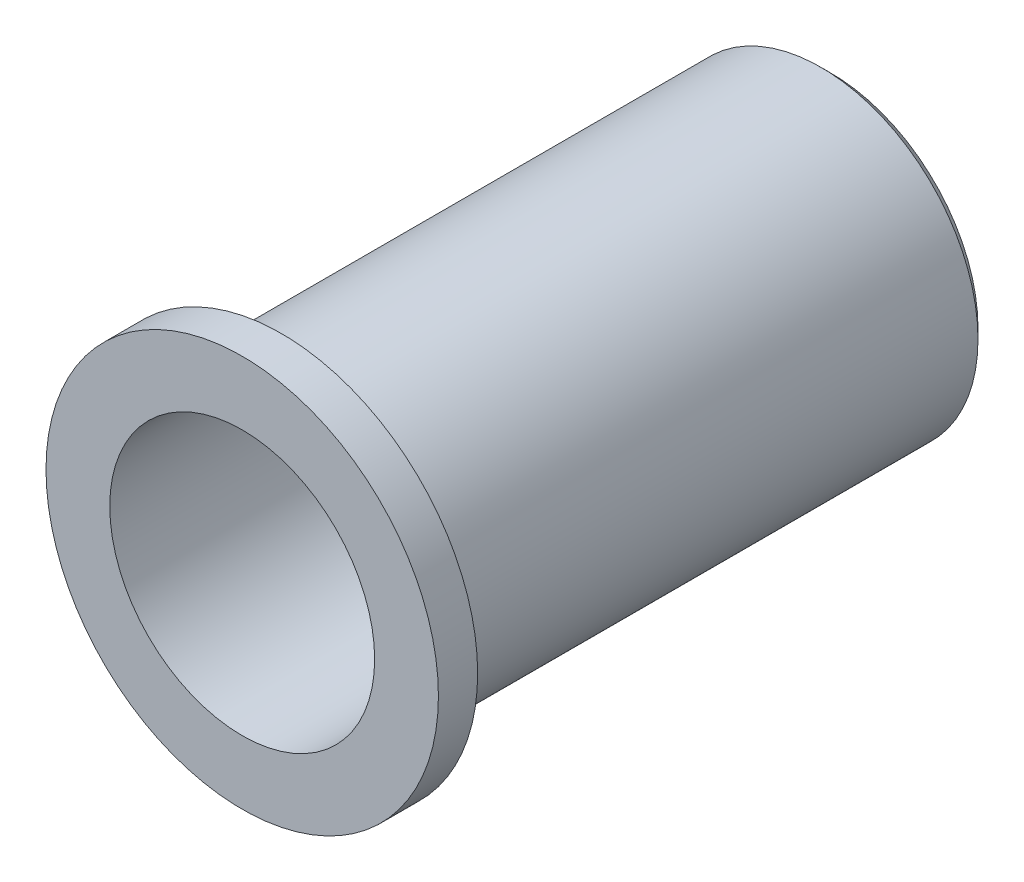
SolidWorks part; units mm, degrees
ref_plane "Спереди" through (0, 0, 0) normal (0, 0, 1) x (1, 0, 0)
ref_plane "Сверху" through (0, 0, 0) normal (0, 1, 0) x (1, 0, 0)
ref_plane "Справа" through (0, 0, 0) normal (1, 0, 0) x (0, 0, -1)
sketch "Эскиз1" plane through (0, 0, 0) normal (0, 0, 1) x (1, 0, 0)
  circle A0 centre (0, 0) radius 4
extrude "Бобышка-Вытянуть1" add sketch "Эскиз1" along normal blind 12
sketch "Эскиз2" plane through (0, 0, 12) normal (0, 0, 1) x (1, 0, 0)
  circle A0 centre (0, 0) radius 2.7
extrude "Вырез-Вытянуть1" cut sketch "Эскиз2" against normal blind 4.2
sketch "Эскиз3" plane through (0, 0, 0) normal (0, 0, -1) x (-1, 0, 0)
  circle A0 centre (0, 0) radius 3.2
extrude "Вырез-Вытянуть2" cut sketch "Эскиз3" against normal blind 11.2 flip side to cut
sketch "Эскиз4" plane through (0, 0, 0) normal (0, 0, -1) x (-1, 0, 0)
  circle A0 centre (0, 0) radius 1.6
extrude "Вырез-Вытянуть3" cut sketch "Эскиз4" against normal blind 11.2
chamfer "Фаска1" distance 0.2 angle 45 1 edges at (-3.2, 0, 0)
